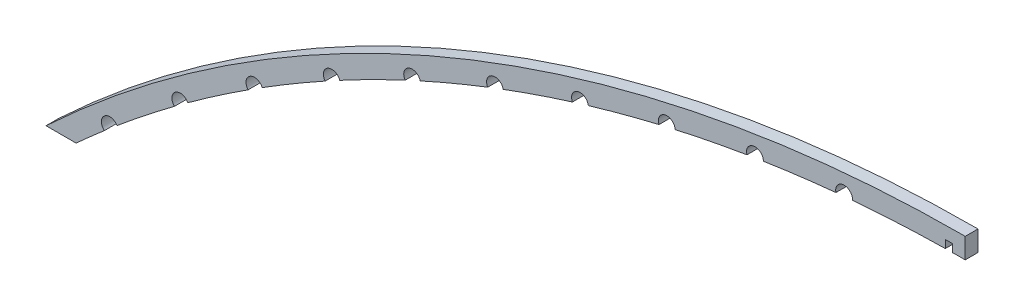
SolidWorks part; units mm, degrees
ref_plane "Front Plane" through (0, 0, 0) normal (0, 0, 1) x (1, 0, 0)
ref_plane "Top Plane" through (0, 0, 0) normal (0, 1, 0) x (1, 0, 0)
ref_plane "Right Plane" through (0, 0, 0) normal (1, 0, 0) x (0, 0, -1)
sketch "Sketch1" plane through (0, 0, 0) normal (0, 0, 1) x (1, 0, 0)
  line L0 (0, 0) -> (228.6, 0)
  line L1 (40.0294, 9.525) -> (209.55, 9.525)
  line L2 (228.6, 90.4875) -> (228.6, 0)
  line L3 (228.6, 90.4875) -> (200.0199, 90.4875) construction
  line L4 (219.075, 19.05) -> (219.075, 74.3589)
  arc A0 (0, 0) -> (228.6, 90.4875) centre (228.6, -243.5141) cw
  arc A1 (38.1474, 15.2571) -> (215.7733, 77.5314) centre (228.6, -243.5141) cw
  arc A2 (209.55, 9.525) -> (219.075, 19.05) centre (209.55, 19.05) ccw
  arc A3 (8.6922, -9.2593) -> (228.6, 77.7875) centre (228.6, -243.5141) cw construction
  arc A4 (219.075, 74.3589) -> (215.7733, 77.5314) centre (215.9, 74.3589) ccw
  arc A5 (40.0294, 9.525) -> (38.1474, 15.2571) centre (40.0294, 12.7) cw
  dimension "D6" = 9.525
  dimension "D7" = 3.175
  dimension "D1" = 90.4875
  dimension "D2" = 228.6
  dimension "D4" = 9.525
  dimension "D5" = 9.525
  dimension "D3" = 12.7
extrude "Extrude1" add sketch "Sketch1" along normal blind 3.175
sketch "Sketch3" plane through (0, 0, 3.175) normal (0, 0, 1) x (1, 0, 0)
  circle A0 centre (15.875, 7.7755) radius 2.0955
  arc A4 (228.6, 85.725) -> (3.2596, -3.4722) centre (228.6, -243.5141) ccw
  arc A5 (228.6, 85.725) -> (3.2596, -3.4722) centre (228.6, -243.5141) ccw construction
  dimension "D1" = 4.191
  dimension "D3" = 15.875
  dimension "D2" = 4.7625
extrude "Extrude2" cut sketch "Sketch3" against normal through all
ref_axis "Axis1" through (228.6, -243.5141, 3.175) along (0, 0, -1)
pattern_circular "CirPattern1" count 10 over 35 about axis through (228.6, -243.5141, 0) along (0, 0, 1) of "Extrude2"
sketch "Sketch4" plane through (0, 0, 3.175) normal (0, 0, 1) x (1, 0, 0)
  arc A2 (228.6, 85.4075) -> (3.4769, -3.7037) centre (228.6, -243.5141) ccw
  arc A3 (228.6, 85.4075) -> (3.4769, -3.7037) centre (228.6, -243.5141) ccw
  dimension "D1" = 5.08
extrude "Extrude3" cut sketch "Sketch4" against normal through all and the other way through all
sketch "Sketch5" plane through (0, 0, 3.175) normal (0, 0, 1) x (1, 0, 0)
  line L0 (228.6, 85.4075) -> (228.6, 90.4875) construction
  line L1 (223.647, 85.3702) -> (225.425, 85.3702)
  line L2 (223.647, 85.3702) -> (223.647, 87.332)
  line L3 (223.647, 87.332) -> (225.425, 87.332)
  line L4 (225.425, 85.3702) -> (225.425, 87.332)
  arc A0 (228.6, 85.4075) -> (200.571, 84.2111) centre (228.6, -243.5141) ccw construction
  dimension "D1" = 3.175
  dimension "D2" = 1.778
extrude "Extrude4" cut sketch "Sketch5" against normal through all
sketch "Sketch6" plane through (0, 0, 3.175) normal (0, 0, 1) x (1, 0, 0)
  line L0 (14.5042, 6.1906) -> (17.6645, 8.8658) construction
  line L1 (14.5042, 6.1906) -> (19.7447, 0)
  line L2 (17.6645, 8.8658) -> (20.1262, 5.9578)
  line L3 (42.231, 27.5136) -> (44.37, 24.3606)
  line L4 (42.231, 27.5136) -> (45.6575, 29.8381) construction
  line L5 (45.6575, 29.8381) -> (47.7965, 26.6852)
  line L6 (72.0652, 45.7717) -> (73.8573, 42.4094)
  line L7 (72.0652, 45.7717) -> (75.7192, 47.7193) construction
  line L8 (75.7192, 47.7193) -> (77.5113, 44.357)
  line L9 (103.6697, 60.7585) -> (105.0946, 57.2249)
  line L10 (103.6697, 60.7585) -> (107.5098, 62.3071) construction
  line L11 (107.5098, 62.3071) -> (108.9347, 58.7735)
  line L12 (136.6868, 72.3045) -> (137.7285, 68.6396)
  line L13 (136.6868, 72.3045) -> (140.6697, 73.4365) construction
  line L14 (140.6697, 73.4365) -> (141.7113, 69.7716)
  line L15 (170.7434, 80.2791) -> (171.39, 76.5243)
  line L16 (170.7434, 80.2791) -> (174.824, 80.9818) construction
  line L17 (174.824, 80.9818) -> (175.4705, 77.2269)
  line L18 (205.4543, 84.5921) -> (205.6984, 80.7899)
  line L19 (205.4543, 84.5921) -> (209.5863, 84.8575) construction
  line L20 (209.5863, 84.8575) -> (209.8305, 81.0552)
  line L21 (240.4268, 85.1948) -> (240.2659, 81.3881)
  line L22 (240.4268, 85.1948) -> (244.5637, 85.0199) construction
  line L23 (244.5637, 85.0199) -> (244.4028, 81.2132)
  line L24 (228.6, 81.5975) -> (228.6, 85.4075)
  line L25 (7.4885, 0) -> (19.7447, 0)
  line L26 (0, 0) -> (7.4885, 0) construction
  line L27 (19.7447, 0) -> (20.1262, 5.9578)
  line L30 (275.2657, 82.0803) -> (274.7014, 78.3123)
  line L31 (275.2657, 82.0803) -> (279.3606, 81.4671)
  line L32 (279.3606, 81.4671) -> (278.7963, 77.699)
  line L33 (334.802, 172.0372) -> (333.8408, 168.3504)
  line L34 (309.5768, 75.2839) -> (313.5834, 74.2393)
  line L35 (313.5834, 74.2393) -> (312.6222, 70.5525)
  arc A0 (105.0946, 57.2249) -> (20.1262, 5.9578) centre (228.6, -243.5141) ccw
  arc A2 (228.6, 81.5975) -> (6.0846, -6.4815) centre (228.6, -243.5141) ccw
  arc A3 (228.6, 81.5975) -> (240.2659, 81.3881) centre (228.6, -243.5141) ccw
  arc A4 (73.8573, 42.4094) -> (47.7965, 26.6852) centre (228.6, -243.5141) ccw
  arc A5 (105.0946, 57.2249) -> (73.8573, 42.4094) centre (228.6, -243.5141) ccw
  arc A6 (137.7285, 68.6396) -> (105.0946, 57.2249) centre (228.6, -243.5141) ccw
  arc A7 (171.39, 76.5243) -> (141.7113, 69.7716) centre (228.6, -243.5141) ccw
  arc A8 (205.6984, 80.7899) -> (171.39, 76.5243) centre (228.6, -243.5141) ccw
  arc A9 (240.2659, 81.3881) -> (205.6984, 80.7899) centre (228.6, -243.5141) ccw
  point P0 (228.6, -243.5141)
  arc M2 (156.4773, 77.4029) -> (174.3205, 80.8979) centre (228.6, -243.5141) cw
  line M3 (223.647, 85.3702) -> (223.647, 87.332)
  line M4 (223.647, 87.332) -> (225.425, 87.332)
  line M5 (225.425, 87.332) -> (225.425, 85.3922)
  arc M6 (225.425, 85.3922) -> (228.6, 85.4075) centre (228.6, -243.5141) cw
  arc M10 (7.4885, 0) -> (14.5042, 6.1906) centre (228.6, -243.5141) cw
  arc M12 (17.6645, 8.8658) -> (31.9326, 20.136) centre (228.6, -243.5141) cw
  arc M14 (35.267, 22.5908) -> (50.2667, 32.8672) centre (228.6, -243.5141) cw
  arc M16 (53.7599, 35.0902) -> (69.422, 44.3257) centre (228.6, -243.5141) cw
  arc M18 (73.058, 46.3067) -> (89.3103, 54.4587) centre (228.6, -243.5141) cw
  arc M20 (93.0723, 56.1885) -> (109.8401, 63.2195) centre (228.6, -243.5141) cw
  arc M22 (113.7107, 64.6902) -> (130.9168, 70.5677) centre (228.6, -243.5141) cw
  arc M24 (134.8782, 71.7725) -> (152.4433, 76.4696) centre (228.6, -243.5141) cw
  dimension "D1" = 8.89
extrude "Extrude5" [suppressed] add sketch "Sketch6" against normal through all separate body contours A9 L21 L20 M24 | A3 L24 L23 M6 M5 M4 M3 M2 | A8 L18 L17 M22 | A7 L15 L14 M20 | A6 L12 L11 M18 | A0 L9 L8 M16 | A0 L6 L5 M14 | A0 L3 L2 M12 | L25 L1 M10
